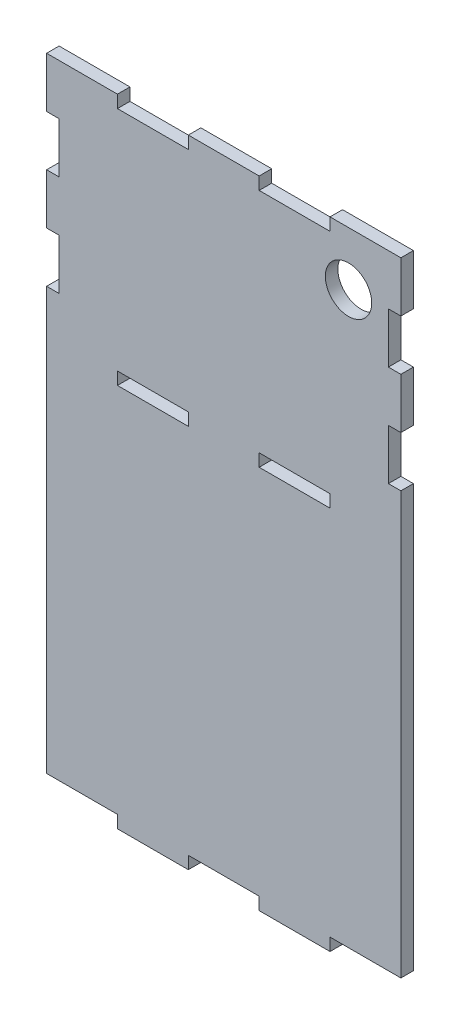
SolidWorks part; units mm, degrees
ref_plane "Ön Düzlem" through (0, 0, 0) normal (0, 0, 1) x (1, 0, 0)
ref_plane "Üst Düzlem" through (0, 0, 0) normal (0, 1, 0) x (1, 0, 0)
ref_plane "Sağ Düzlem" through (0, 0, 0) normal (1, 0, 0) x (0, 0, -1)
sketch "Sketch1" plane through (0, 0, 0) normal (0, 0, 1) x (1, 0, 0)
  line L3 (38.2, 27.2) -> (22.92, 27.2)
  line L7 (7.64, 27.2) -> (-7.64, 27.2)
  line L9 (-22.92, 27.2) -> (-38.2, 27.2)
  line L10 (-38.2, 27.2) -> (-38.2, 16.32)
  line L11 (38.2, 27.2) -> (38.2, 16.32)
  line L12 (-22.92, 24.5) -> (-7.64, 24.5)
  line L13 (-38.2, 5.44) -> (-38.2, -5.44)
  line L14 (7.64, 24.5) -> (22.92, 24.5)
  line L16 (-22.92, 27.2) -> (-22.92, 24.5)
  line L17 (-7.64, 27.2) -> (-7.64, 24.5)
  line L18 (7.64, 24.5) -> (7.64, 27.2)
  line L19 (22.92, 27.2) -> (22.92, 24.5)
  line L21 (-7.64, -24.5) -> (-22.92, -24.5)
  line L23 (22.92, -24.5) -> (22.92, -27.2)
  line L25 (38.2, 5.44) -> (38.2, -5.44)
  line L26 (7.64, -27.2) -> (7.64, -24.5)
  line L28 (-22.92, -24.5) -> (-22.92, -27.2)
  line L30 (22.92, -24.5) -> (7.64, -24.5)
  line L33 (-7.64, -24.5) -> (-7.64, -27.2)
  line L35 (35.5, 5.44) -> (35.5, 16.32)
  line L37 (35.5, -16.32) -> (35.5, -5.44)
  line L38 (-35.5, -16.32) -> (-35.5, -5.44)
  line L39 (22.92, -107.3) -> (22.92, -110)
  line L40 (-35.5, 5.44) -> (-35.5, 16.32)
  line L42 (-38.2, 5.44) -> (-35.5, 5.44)
  line L43 (-38.2, -5.44) -> (-35.5, -5.44)
  line L44 (-38.2, -16.32) -> (-35.5, -16.32)
  line L45 (35.5, -16.32) -> (38.2, -16.32)
  line L46 (-38.2, 16.32) -> (-35.5, 16.32)
  line L47 (35.5, -5.44) -> (38.2, -5.44)
  line L48 (35.5, 5.44) -> (38.2, 5.44)
  line L49 (35.5, 16.32) -> (38.2, 16.32)
  line L52 (-7.64, -107.3) -> (-7.64, -110)
  line L53 (7.64, -110) -> (7.64, -107.3)
  line L55 (-22.92, -107.3) -> (-22.92, -110)
  line L59 (22.92, -27.2) -> (7.64, -27.2)
  line L60 (-7.64, -27.2) -> (-22.92, -27.2)
  line L61 (38.2, -107.3) -> (38.2, -16.32)
  line L62 (-38.2, -16.32) -> (-38.2, -107.3)
  line L63 (-22.92, -110) -> (-7.64, -110)
  line L66 (7.64, -107.3) -> (-7.64, -107.3)
  line L67 (7.64, -110) -> (22.92, -110)
  line L68 (-22.92, -107.3) -> (-38.2, -107.3)
  line L69 (22.92, -107.3) -> (38.2, -107.3)
  circle A0 centre (26.9081, 15.5995) radius 5
  point P0 (0, 0)
  dimension "D1" = 76.4
extrude "Boss-Extrude1" add sketch "Sketch1" against normal blind 2.7
